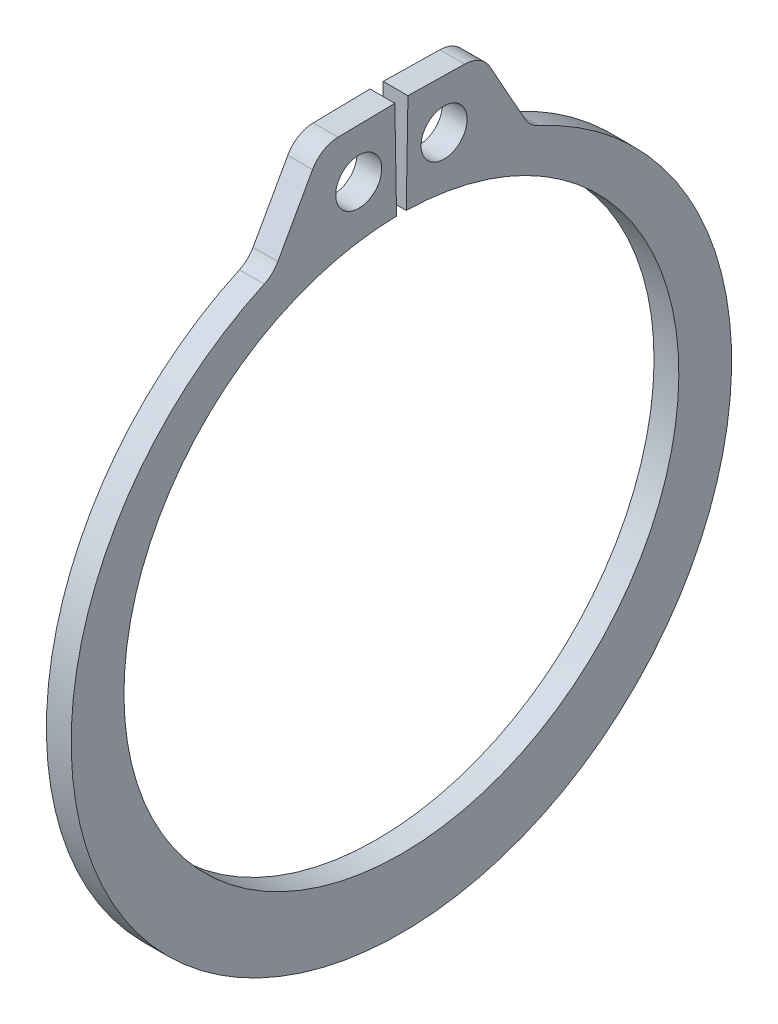
SolidWorks part; units mm, degrees
material "Cast Carbon Steel"
ref_plane "Front" through (0, 0, 0) normal (0, 0, 1) x (1, 0, 0)
ref_plane "Top" through (0, 0, 0) normal (0, 1, 0) x (1, 0, 0)
ref_plane "Right" through (0, 0, 0) normal (1, 0, 0) x (0, 0, -1)
sketch "Sketch1" plane through (0, 0, 0) normal (1, 0, 0) x (0, 0, -1)
  line L0 (0, 0) -> (0, 11.938) construction
  line L1 (-0.2083, 11.9362) -> (-0.2824, 16.1773)
  line L2 (0.2824, 16.1773) -> (3.4632, 16.1218)
  line L3 (3.4632, 16.1218) -> (5.5253, 12.415)
  line L4 (0.2083, 11.9362) -> (0.2824, 16.1773)
  line L5 (-0.2824, 16.1773) -> (-3.4632, 16.1218)
  line L6 (-3.4632, 16.1218) -> (-5.5253, 12.415)
  line L7 (-5.5253, 12.415) -> (-4.854, 10.9066) construction
  line L8 (5.5253, 12.415) -> (4.854, 10.9066) construction
  line L9 (0, -11.938) -> (0, -14.8844) construction
  line L10 (-3.4632, 16.1218) -> (-0.2083, 11.9362) construction
  line L11 (0, 11.938) -> (0, 16.1798) construction
  line L12 (-11.938, 0) -> (11.938, 0) construction
  circle A0 centre (0, 0) radius 11.938 construction
  arc A1 (-0.2083, 11.9362) -> (0.2083, 11.9362) centre (0, 0) ccw
  circle A3 centre (0, 0) radius 17.526 construction
  circle A4 centre (-1.8358, 14.029) radius 0.9906
  circle A5 centre (1.8358, 14.029) radius 0.9906
  arc A6 (-5.5253, 12.415) -> (5.5253, 12.415) centre (0, -0.6756) ccw
  point P0 (0, -14.8844)
  dimension "A" = 23.876
  dimension "D2" = 3.1813
  dimension "L" = 35.052
  dimension "Hole" = 1.9812
  dimension "Smin" = 1.651
  dimension "Smax" = 2.9464
  dimension "H" = 4.2418
  dimension "Angle" = 1
extrude "Extrude1" add sketch "Sketch1" along normal mid plane 1.0668
fillet "Fillet1" radius 1.2827 4 edges at (0, 12.415, 5.5253) (0, 12.415, -5.5253) (0, 16.1218, 3.4632) (0, 16.1218, -3.4632)
sketch "Sketch2" plane through (0, 0, 0) normal (0, 0, 1) x (1, 0, 0)
  line L0 (-5.9182, 0) -> (15.4178, 0)
  line L1 (15.4178, 0) -> (15.4178, -12.7)
  line L2 (-0.5842, -12.7) -> (-5.1562, -12.7)
  line L3 (15.4178, -12.7) -> (0.5842, -12.7)
  line L4 (0.5842, -12.7) -> (0.5842, -11.938)
  line L5 (0.5842, -11.938) -> (-0.5842, -11.938)
  line L6 (-0.5842, -11.938) -> (-0.5842, -12.7)
  line L7 (-0.5842, -12.7) -> (-5.9182, -12.7) construction
  line L8 (-5.9182, -12.7) -> (-5.9182, 0) construction
  line L9 (15.4178, 0) -> (76.391, 0) construction
  line L10 (-5.1562, -12.7) -> (-5.9182, -11.938)
  line L11 (-5.9182, -11.938) -> (-5.9182, 0)
  point P10 (0, -11.938)
  dimension "D1" = 45
  dimension "Dg" = 23.876
  dimension "Ds" = 25.4
  dimension "W" = 1.1684
  dimension "D2" = 21.336
  dimension "D3" = 5.334
revolve "Revolve1" [suppressed] add sketch "Sketch2" angle 360 about L9
delete or keep bodies "Body-Delete1" [suppressed] type delete bodies bodies 122
equation "\"D2@Sketch2\" = \"D1@Extrude1\"*20"
equation "\"D3@Sketch2\" = \"D2@Sketch2\"/4"
equation "\"D2@Sketch1\" = \"H@Sketch1\"*.75"
